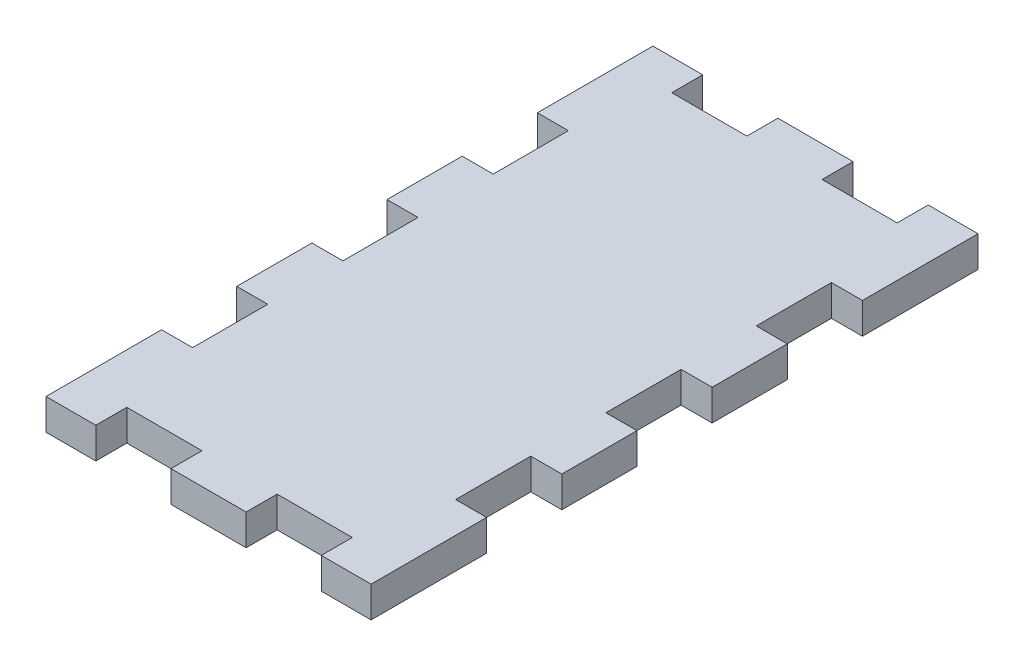
SolidWorks part; units mm, degrees
ref_plane "Plan de face" through (0, 0, 0) normal (0, 0, 1) x (1, 0, 0)
ref_plane "Plan de dessus" through (0, 0, 0) normal (0, 1, 0) x (1, 0, 0)
ref_plane "Plan de droite" through (0, 0, 0) normal (1, 0, 0) x (0, 0, -1)
sketch "Esquisse1" plane through (0, 0, 0) normal (0, 1, 0) x (1, 0, 0)
  line L1 (-17.3, 32.3) -> (17.3, 32.3)
  line L2 (-17.3, 32.3) -> (-17.3, -32.3)
  line L3 (-17.3, -32.3) -> (17.3, -32.3)
  line L4 (17.3, 32.3) -> (17.3, -32.3)
  line L5 (-17.3, 32.3) -> (17.3, -32.3) construction
  line L6 (-17.3, -32.3) -> (17.3, 32.3) construction
  point P0 (0, 0)
  dimension "D1" = 64.6
  dimension "D2" = 34.6
extrude "Boss.-Extru.1" add sketch "Esquisse1" along normal blind 3.3
sketch "Esquisse2" plane through (0, 3.3, 0) normal (0, 1, 0) x (1, 0, 0)
  line L1 (-4, 32.3) -> (4, 32.3) construction
  line L2 (-4, 32.3) -> (-4, 29)
  line L3 (-4, 29) -> (4, 29) construction
  line L4 (4, 32.3) -> (4, 29)
  line L5 (17.3, 32.3) -> (-17.3, 32.3) construction
  line L7 (-17.3, 32.3) -> (-12, 32.3) construction
  line L8 (-17.3, 32.3) -> (-17.3, 29) construction
  line L9 (-17.3, 29) -> (-12, 29) construction
  line L10 (-12, 32.3) -> (-12, 29)
  line L11 (17.3, 32.3) -> (12, 32.3) construction
  line L12 (17.3, 32.3) -> (17.3, 29) construction
  line L13 (17.3, 29) -> (12, 29) construction
  line L14 (12, 32.3) -> (12, 29)
  line L15 (-12, 32.3) -> (-4, 32.3)
  line L16 (-12, 32.3) -> (-12, 29)
  line L17 (-12, 29) -> (-4, 29)
  line L18 (-4, 32.3) -> (-4, 29)
  line L19 (4, 32.3) -> (12, 32.3)
  line L20 (4, 32.3) -> (4, 29)
  line L21 (4, 29) -> (12, 29)
  line L22 (12, 32.3) -> (12, 29)
  point P5 (0, 32.3)
  point P8 (0, 32.3)
  line M6 (17.3, 32.3) -> (-17.3, 32.3)
  dimension "D1" = 8
  dimension "D2" = 3.3
  dimension "D3" = 8
extrude "Enlèv. mat.-Extru.1" cut sketch "Esquisse2" against normal through all both and the other way through all contours L10 L17 L2 M6 | L4 L21 L14 M6
mirror "Symétrie1" about plane through (0, 0, 0) normal (0, 0, 1) of "Enlèv. mat.-Extru.1"
sketch "Esquisse3" plane through (0, 3.3, 0) normal (0, 1, 0) x (1, 0, 0)
  line L1 (-17.3, -4) -> (-14, -4)
  line L2 (-17.3, -4) -> (-17.3, 4)
  line L3 (-17.3, 4) -> (-14, 4)
  line L4 (-14, -4) -> (-14, 4)
  line L5 (-17.3, 32.3) -> (-17.3, -32.3) construction
  line L7 (-17.3, 20) -> (-14, 20)
  line L8 (-17.3, 20) -> (-17.3, 12)
  line L9 (-17.3, 12) -> (-14, 12)
  line L10 (-14, 20) -> (-14, 12)
  line L11 (-17.3, -12) -> (-14, -12)
  line L12 (-17.3, -12) -> (-17.3, -20)
  line L13 (-17.3, -20) -> (-14, -20)
  line L14 (-14, -12) -> (-14, -20)
  point P5 (-17.3, 0)
  point P8 (-17.3, 0)
  dimension "D1" = 3.3
  dimension "D2" = 8
  dimension "D3" = 8
  dimension "D4" = 8
extrude "Enlèv. mat.-Extru.2" cut sketch "Esquisse3" against normal blind 3.3
mirror "Symétrie2" about plane through (0, 0, 0) normal (1, 0, 0) of "Enlèv. mat.-Extru.2"
